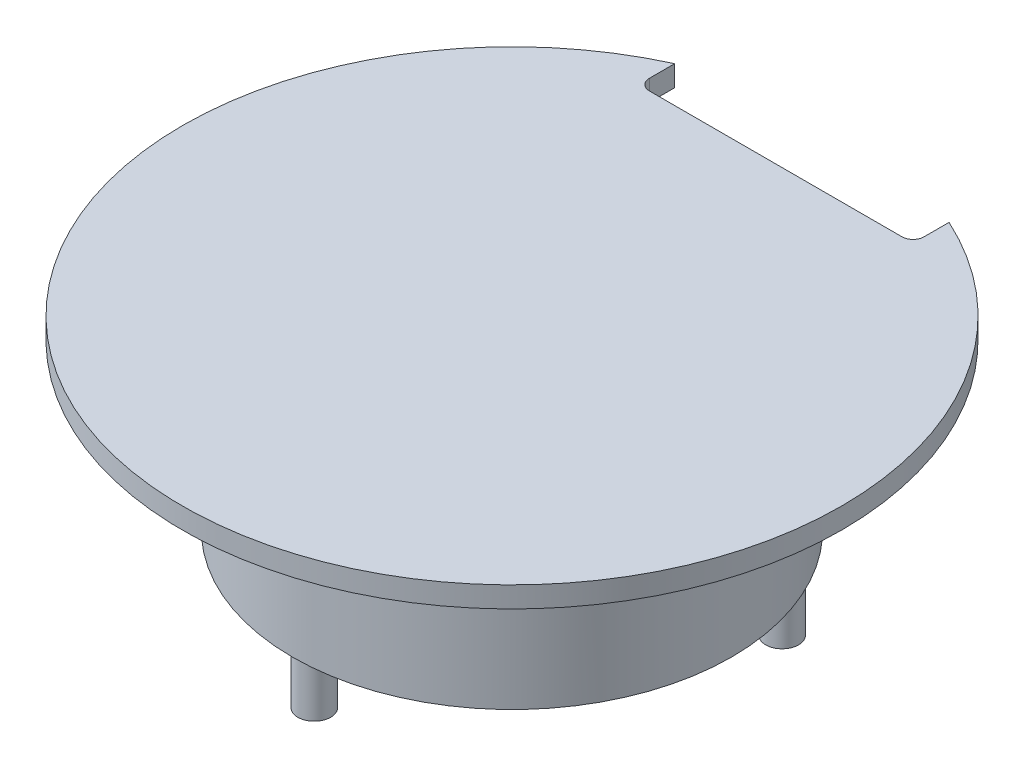
SolidWorks part; units mm, degrees
ref_plane "Front Plane" through (0, 0, 0) normal (0, 0, 1) x (1, 0, 0)
ref_plane "Top Plane" through (0, 0, 0) normal (0, 1, 0) x (1, 0, 0)
ref_plane "Right Plane" through (0, 0, 0) normal (1, 0, 0) x (0, 0, -1)
sketch "Sketch2" plane through (0, 0, 0) normal (0, 0, 1) x (1, 0, 0)
  line L0 (1.5, -20) -> (1.5, -5)
  line L5 (1.5, -5) -> (11.5, -5)
  line L12 (-18.5, -3.1) -> (-18.5, -5.1)
  line L13 (-2.5, -20) -> (1.5, -20)
  line L14 (-18.5, -5.1) -> (-2.5, -5.1)
  line L15 (-2.5, -5.1) -> (-2.5, -20)
  line L23 (11.5, -5) -> (11.5, -3.1)
  line L25 (-18.5, -3.1) -> (11.5, -3.1)
  dimension "D1" = 30
  dimension "D3" = 15
  dimension "D6" = 2
  dimension "4mm" = 4
  dimension "D7" = 16
revolve "Revolve3" add sketch "Sketch2" angle 360 about L12
sketch "Sketch4" plane through (0, -20, 0) normal (0, -1, 0) x (1, 0, 0)
  circle A3 centre (-2.9115, -9) radius 1.5
  circle A4 centre (-18.5, 18) radius 1.5
  circle A5 centre (-34.0885, -9) radius 1.5
  point P0 (0, 0)
  point P7 (-18.5, 0)
extrude "Boss-Extrude1" add sketch "Sketch4" along normal blind 5
sketch "Sketch5" plane through (0, -3.1, 0) normal (0, 1, 0) x (1, 0, 0)
  line L8 (-30.9754, 23.979) -> (-5.9754, 23.979)
  line L9 (-30.9754, 23.979) -> (-30.9754, 30.6)
  line L10 (-30.9754, 30.6) -> (-5.9754, 30.6)
  line L11 (-5.9754, 23.979) -> (-5.9754, 30.6)
  line L12 (-30.9754, 23.979) -> (-5.9754, 30.6) construction
  line L13 (-30.9754, 30.6) -> (-5.9754, 23.979) construction
  point P8 (-18.4754, 27.2895)
extrude "Cut-Extrude5" cut sketch "Sketch5" against normal blind 5 contours L9 L10 L11 L8
fillet "Fillet1" radius 1 2 edges at (-5.9754, -4.05, -23.979) (-30.9754, -4.05, -23.979)
sketch "Sketch6" plane through (0, 0, -23.979) normal (0, 0, -1) x (-1, 0, 0)
  line L0 (18.4754, -3.1) -> (18.5, -20) construction
  line L1 (29.9754, -3.1) -> (6.9754, -3.1) construction
  line L2 (17, -20) -> (20, -20) construction
  line L3 (9.4877, -11.55) -> (27.4877, -11.55)
  line L4 (9.4877, -11.55) -> (9.4877, -5)
  line L5 (-1.5, -5) -> (38.5, -5) construction
  line L7 (27.4877, -5) -> (27.4877, -11.55)
  point P6 (0, 0)
  point P9 (18.4877, -11.55)
  point P14 (0, 0)
  point P15 (0, 0)
  line M4 (6.9754, -5) -> (29.9754, -5)
  dimension "D1" = 18
extrude "Cut-Extrude9" cut sketch "Sketch6" against normal blind 15 and the other way through all contours L0 L4 L3 M4 | L0 L3 L7 M4
other "Move Face1" face at (-18.4945, -5.1, -3.7967) parameters "D1"=0.1
